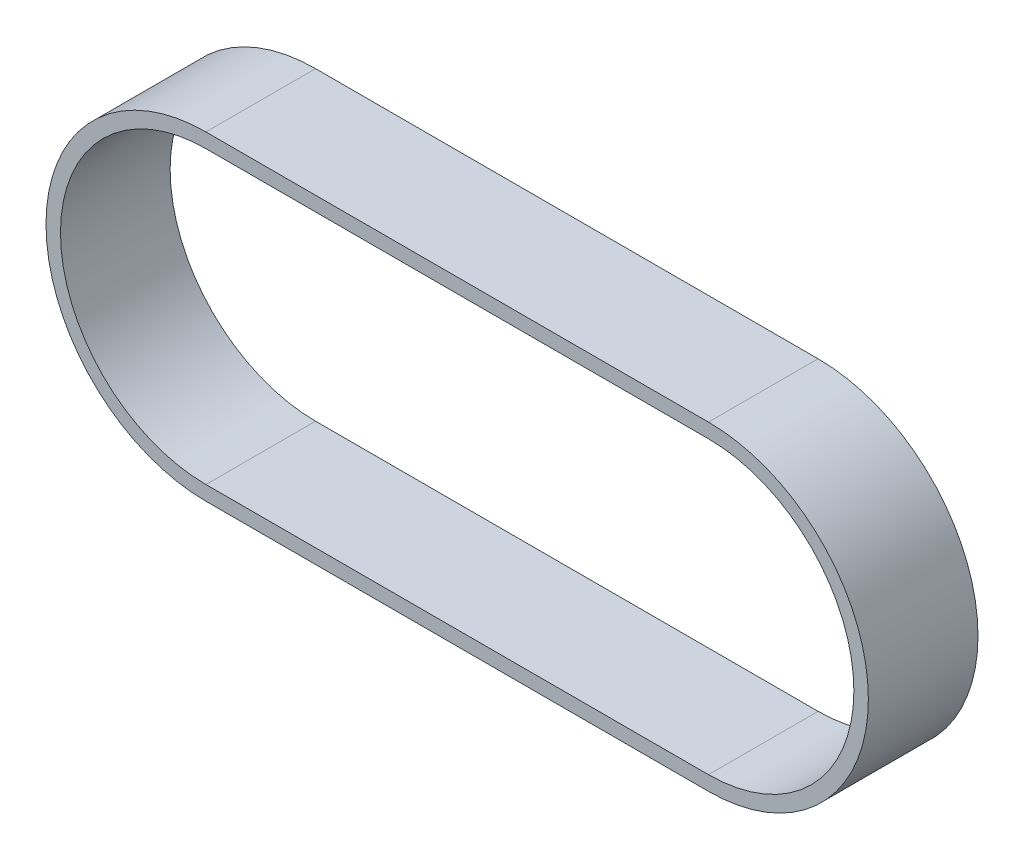
SolidWorks part; units mm, degrees
ref_plane "Plan de face" through (0, 0, 0) normal (0, 0, 1) x (1, 0, 0)
ref_plane "Plan de dessus" through (0, 0, 0) normal (0, 1, 0) x (1, 0, 0)
ref_plane "Plan de droite" through (0, 0, 0) normal (1, 0, 0) x (0, 0, -1)
sketch "Esquisse1" plane through (0, 0, 0) normal (0, 0, 1) x (1, 0, 0)
  line L1 (0, 15.915) -> (55, 15.915)
  line L2 (0, 17.5) -> (55, 17.5)
  line L3 (0, 0) -> (29.489, 0) construction
  line L4 (0, -17.5) -> (55, -17.5)
  line L5 (0, -15.915) -> (55, -15.915)
  arc A0 (0, 15.915) -> (0, -15.915) centre (0, 0) ccw
  arc A1 (55, -15.915) -> (55, 15.915) centre (55, 0) ccw
  arc A2 (0, 17.5) -> (0, -17.5) centre (0, 0) ccw
  arc A3 (55, -17.5) -> (55, 17.5) centre (55, 0) ccw
extrude "Extrusion1" add sketch "Esquisse1" along normal blind 12
